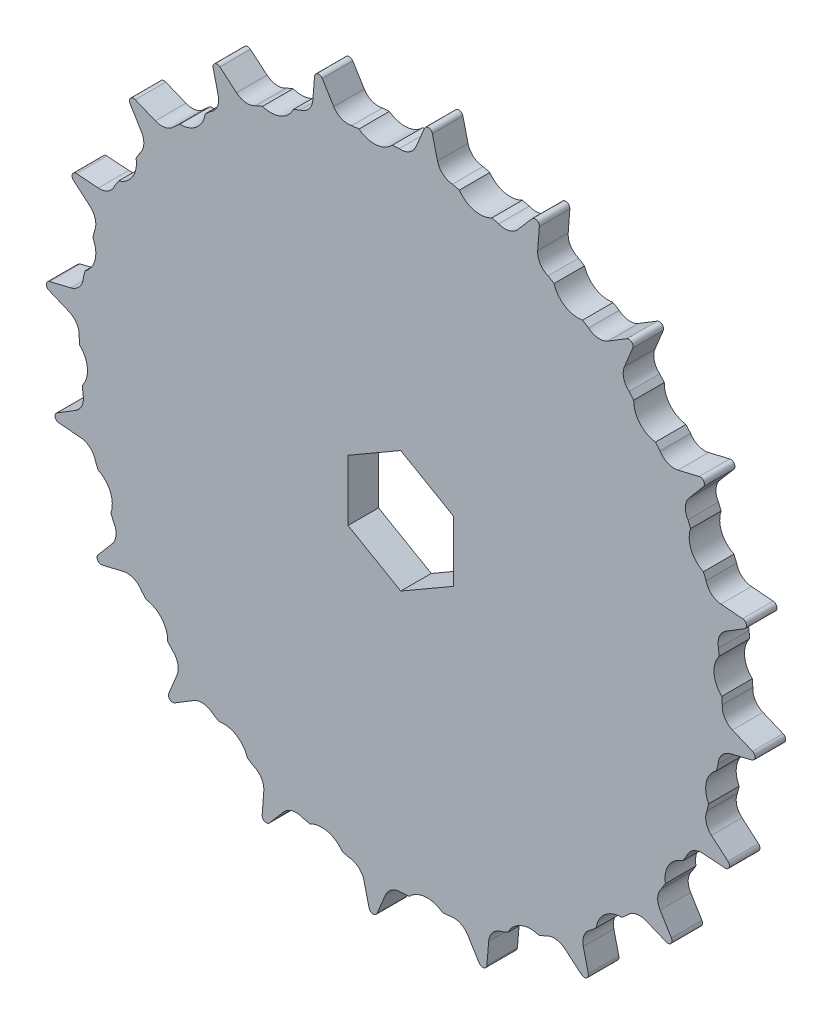
SolidWorks part; units mm, degrees
ref_plane "Front Plane" through (0, 0, 0) normal (0, 0, 1) x (1, 0, 0)
ref_plane "Top Plane" through (0, 0, 0) normal (0, 1, 0) x (1, 0, 0)
ref_plane "Right Plane" through (0, 0, 0) normal (1, 0, 0) x (0, 0, -1)
sketch "Sketch1" plane through (0, 0, 0) normal (0, 0, 1) x (1, 0, 0)
  line L0 (3.6626, 79.3215) -> (5.6677, 84.1262)
  line L1 (3.6626, 79.3215) -> (8.7911, 78.9179) construction
  line L2 (7.5623, 83.9771) -> (8.7911, 78.9179)
  line L3 (3.6626, 79.3215) -> (0, 0) construction
  line L4 (0, 0) -> (8.7911, 78.9179) construction
  line L5 (16.0261, 77.772) -> (18.7582, 82.2038)
  line L6 (20.6061, 81.7602) -> (21.0283, 76.5711)
  line L7 (27.995, 74.3074) -> (31.3867, 78.2573)
  line L8 (33.1425, 77.5301) -> (32.7478, 72.3388)
  line L9 (39.2746, 69.0132) -> (43.2424, 72.3839)
  line L10 (44.8629, 71.3909) -> (43.6609, 66.3253)
  line L11 (49.5871, 62.0196) -> (54.0334, 64.7281)
  line L12 (55.4785, 63.4939) -> (53.4989, 58.6786)
  line L13 (58.6786, 53.4989) -> (63.4939, 55.4785)
  line L14 (64.7281, 54.0334) -> (62.0196, 49.5871)
  line L15 (66.3253, 43.6609) -> (71.3909, 44.8629)
  line L16 (72.3839, 43.2424) -> (69.0132, 39.2746)
  line L17 (72.3388, 32.7478) -> (77.5301, 33.1425)
  line L18 (78.2573, 31.3867) -> (74.3074, 27.995)
  line L19 (76.5711, 21.0283) -> (81.7602, 20.6061)
  line L20 (82.2038, 18.7582) -> (77.772, 16.0261)
  line L21 (78.9179, 8.7911) -> (83.9771, 7.5623)
  line L22 (84.1262, 5.6677) -> (79.3215, 3.6626)
  line L23 (79.3215, -3.6626) -> (84.1262, -5.6677)
  line L24 (83.9771, -7.5623) -> (78.9179, -8.7911)
  line L25 (77.772, -16.0261) -> (82.2038, -18.7582)
  line L26 (81.7602, -20.6061) -> (76.5711, -21.0283)
  line L27 (74.3074, -27.995) -> (78.2573, -31.3867)
  line L28 (77.5301, -33.1425) -> (72.3388, -32.7478)
  line L29 (69.0132, -39.2746) -> (72.3839, -43.2424)
  line L30 (71.3909, -44.8629) -> (66.3253, -43.6609)
  line L31 (62.0196, -49.5871) -> (64.7281, -54.0334)
  line L32 (63.4939, -55.4785) -> (58.6786, -53.4989)
  line L33 (53.4989, -58.6786) -> (55.4785, -63.4939)
  line L34 (54.0334, -64.7281) -> (49.5871, -62.0196)
  line L35 (43.6609, -66.3253) -> (44.8629, -71.3909)
  line L36 (43.2424, -72.3839) -> (39.2746, -69.0132)
  line L37 (32.7478, -72.3388) -> (33.1425, -77.5301)
  line L38 (31.3867, -78.2573) -> (27.995, -74.3074)
  line L39 (21.0283, -76.5711) -> (20.6061, -81.7602)
  line L40 (18.7582, -82.2038) -> (16.0261, -77.772)
  line L41 (8.7911, -78.9179) -> (7.5623, -83.9771)
  line L42 (5.6677, -84.1262) -> (3.6626, -79.3215)
  line L43 (-3.6626, -79.3215) -> (-5.6677, -84.1262)
  line L44 (-7.5623, -83.9771) -> (-8.7911, -78.9179)
  line L45 (-16.0261, -77.772) -> (-18.7582, -82.2038)
  line L46 (-20.6061, -81.7602) -> (-21.0283, -76.5711)
  line L47 (-27.995, -74.3074) -> (-31.3867, -78.2573)
  line L48 (-33.1425, -77.5301) -> (-32.7478, -72.3388)
  line L49 (-39.2746, -69.0132) -> (-43.2424, -72.3839)
  line L50 (-44.8629, -71.3909) -> (-43.6609, -66.3253)
  line L51 (-49.5871, -62.0196) -> (-54.0334, -64.7281)
  line L52 (-55.4785, -63.4939) -> (-53.4989, -58.6786)
  line L53 (-58.6786, -53.4989) -> (-63.4939, -55.4785)
  line L54 (-64.7281, -54.0334) -> (-62.0196, -49.5871)
  line L55 (-66.3253, -43.6609) -> (-71.3909, -44.8629)
  line L56 (-72.3839, -43.2424) -> (-69.0132, -39.2746)
  line L57 (-72.3388, -32.7478) -> (-77.5301, -33.1425)
  line L58 (-78.2573, -31.3867) -> (-74.3074, -27.995)
  line L59 (-76.5711, -21.0283) -> (-81.7602, -20.6061)
  line L60 (-82.2038, -18.7582) -> (-77.772, -16.0261)
  line L61 (-78.9179, -8.7911) -> (-83.9771, -7.5623)
  line L62 (-84.1262, -5.6677) -> (-79.3215, -3.6626)
  line L63 (-79.3215, 3.6626) -> (-84.1262, 5.6677)
  line L64 (-83.9771, 7.5623) -> (-78.9179, 8.7911)
  line L65 (-77.772, 16.0261) -> (-82.2038, 18.7582)
  line L66 (-81.7602, 20.6061) -> (-76.5711, 21.0283)
  line L67 (-74.3074, 27.995) -> (-78.2573, 31.3867)
  line L68 (-77.5301, 33.1425) -> (-72.3388, 32.7478)
  line L69 (-69.0132, 39.2746) -> (-72.3839, 43.2424)
  line L70 (-71.3909, 44.8629) -> (-66.3253, 43.6609)
  line L71 (-62.0196, 49.5871) -> (-64.7281, 54.0334)
  line L72 (-63.4939, 55.4785) -> (-58.6786, 53.4989)
  line L73 (-53.4989, 58.6786) -> (-55.4785, 63.4939)
  line L74 (-54.0334, 64.7281) -> (-49.5871, 62.0196)
  line L75 (-43.6609, 66.3253) -> (-44.8629, 71.3909)
  line L76 (-43.2424, 72.3839) -> (-39.2746, 69.0132)
  line L77 (-32.7478, 72.3388) -> (-33.1425, 77.5301)
  line L78 (-31.3867, 78.2573) -> (-27.995, 74.3074)
  line L79 (-21.0283, 76.5711) -> (-20.6061, 81.7602)
  line L80 (-18.7582, 82.2038) -> (-16.0261, 77.772)
  line L81 (-8.7911, 78.9179) -> (-7.5623, 83.9771)
  line L82 (-5.6677, 84.1262) -> (-3.6626, 79.3215)
  line L83 (0, 80.85) -> (0, 0) construction
  line L84 (0, 0) -> (6.5906, 83.7411) construction
  circle A0 centre (0, 0) radius 80.85 construction
  arc A1 (-3.9676, 80.7526) -> (3.6626, 79.3215) centre (0, 80.85) ccw
  arc A2 (4.2537, 80.738) -> (8.4288, 80.4094) centre (0, 0) cw
  arc A3 (5.6677, 84.1262) -> (7.5623, 83.9771) centre (6.5906, 83.7411) cw
  arc A4 (8.7138, 80.3791) -> (16.0261, 77.772) centre (12.6477, 79.8546) ccw
  arc A5 (18.7582, 82.2038) -> (20.6061, 81.7602) centre (19.6094, 81.6791) cw
  arc A6 (21.1806, 78.0263) -> (27.995, 74.3074) centre (24.984, 76.8929) ccw
  arc A7 (31.3867, 78.2573) -> (33.1425, 77.5301) centre (32.1454, 77.6059) cw
  arc A8 (33.1258, 73.7523) -> (39.2746, 69.0132) centre (36.7051, 72.0379) ccw
  arc A9 (43.2424, 72.3839) -> (44.8629, 71.3909) centre (43.8899, 71.6218) cw
  arc A10 (44.2554, 67.6623) -> (49.5871, 62.0196) centre (47.5224, 65.409) ccw
  arc A11 (54.0334, 64.7281) -> (55.4785, 63.4939) centre (54.5536, 63.8741) cw
  arc A12 (54.2952, 59.9062) -> (58.6786, 53.4989) centre (57.1696, 57.1696) ccw
  arc A13 (63.4939, 55.4785) -> (64.7281, 54.0334) centre (63.8741, 54.5536) cw
  arc A14 (62.9981, 50.675) -> (66.3253, 43.6609) centre (65.409, 47.5224) ccw
  arc A15 (71.3909, 44.8629) -> (72.3839, 43.2424) centre (71.6218, 43.8899) cw
  arc A16 (70.1499, 40.196) -> (72.3388, 32.7478) centre (72.0379, 36.7051) ccw
  arc A17 (77.5301, 33.1425) -> (78.2573, 31.3867) centre (77.6059, 32.1454) cw
  arc A18 (75.5742, 28.7273) -> (76.5711, 21.0283) centre (76.8929, 24.984) ccw
  arc A19 (81.7602, 20.6061) -> (82.2038, 18.7582) centre (81.6791, 19.6094) cw
  arc A20 (79.1377, 16.5512) -> (78.9179, 8.7911) centre (79.8546, 12.6477) ccw
  arc A21 (83.9771, 7.5623) -> (84.1262, 5.6677) centre (83.7411, 6.5906) cw
  arc A22 (80.7526, 3.9676) -> (79.3215, -3.6626) centre (80.85, 0) ccw
  arc A23 (84.1262, -5.6677) -> (83.9771, -7.5623) centre (83.7411, -6.5906) cw
  arc A24 (80.3791, -8.7138) -> (77.772, -16.0261) centre (79.8546, -12.6477) ccw
  arc A25 (82.2038, -18.7582) -> (81.7602, -20.6061) centre (81.6791, -19.6094) cw
  arc A26 (78.0263, -21.1806) -> (74.3074, -27.995) centre (76.8929, -24.984) ccw
  arc A27 (78.2573, -31.3867) -> (77.5301, -33.1425) centre (77.6059, -32.1454) cw
  arc A28 (73.7523, -33.1258) -> (69.0132, -39.2746) centre (72.0379, -36.7051) ccw
  arc A29 (72.3839, -43.2424) -> (71.3909, -44.8629) centre (71.6218, -43.8899) cw
  arc A30 (67.6623, -44.2554) -> (62.0196, -49.5871) centre (65.409, -47.5224) ccw
  arc A31 (64.7281, -54.0334) -> (63.4939, -55.4785) centre (63.8741, -54.5536) cw
  arc A32 (59.9062, -54.2952) -> (53.4989, -58.6786) centre (57.1696, -57.1696) ccw
  arc A33 (55.4785, -63.4939) -> (54.0334, -64.7281) centre (54.5536, -63.8741) cw
  arc A34 (50.675, -62.9981) -> (43.6609, -66.3253) centre (47.5224, -65.409) ccw
  arc A35 (44.8629, -71.3909) -> (43.2424, -72.3839) centre (43.8899, -71.6218) cw
  arc A36 (40.196, -70.1499) -> (32.7478, -72.3388) centre (36.7051, -72.0379) ccw
  arc A37 (33.1425, -77.5301) -> (31.3867, -78.2573) centre (32.1454, -77.6059) cw
  arc A38 (28.7273, -75.5742) -> (21.0283, -76.5711) centre (24.984, -76.8929) ccw
  arc A39 (20.6061, -81.7602) -> (18.7582, -82.2038) centre (19.6094, -81.6791) cw
  arc A40 (16.5512, -79.1377) -> (8.7911, -78.9179) centre (12.6477, -79.8546) ccw
  arc A41 (7.5623, -83.9771) -> (5.6677, -84.1262) centre (6.5906, -83.7411) cw
  arc A42 (3.9676, -80.7526) -> (-3.6626, -79.3215) centre (0, -80.85) ccw
  arc A43 (-5.6677, -84.1262) -> (-7.5623, -83.9771) centre (-6.5906, -83.7411) cw
  arc A44 (-8.7138, -80.3791) -> (-16.0261, -77.772) centre (-12.6477, -79.8546) ccw
  arc A45 (-18.7582, -82.2038) -> (-20.6061, -81.7602) centre (-19.6094, -81.6791) cw
  arc A46 (-21.1806, -78.0263) -> (-27.995, -74.3074) centre (-24.984, -76.8929) ccw
  arc A47 (-31.3867, -78.2573) -> (-33.1425, -77.5301) centre (-32.1454, -77.6059) cw
  arc A48 (-33.1258, -73.7523) -> (-39.2746, -69.0132) centre (-36.7051, -72.0379) ccw
  arc A49 (-43.2424, -72.3839) -> (-44.8629, -71.3909) centre (-43.8899, -71.6218) cw
  arc A50 (-44.2554, -67.6623) -> (-49.5871, -62.0196) centre (-47.5224, -65.409) ccw
  arc A51 (-54.0334, -64.7281) -> (-55.4785, -63.4939) centre (-54.5536, -63.8741) cw
  arc A52 (-54.2952, -59.9062) -> (-58.6786, -53.4989) centre (-57.1696, -57.1696) ccw
  arc A53 (-63.4939, -55.4785) -> (-64.7281, -54.0334) centre (-63.8741, -54.5536) cw
  arc A54 (-62.9981, -50.675) -> (-66.3253, -43.6609) centre (-65.409, -47.5224) ccw
  arc A55 (-71.3909, -44.8629) -> (-72.3839, -43.2424) centre (-71.6218, -43.8899) cw
  arc A56 (-70.1499, -40.196) -> (-72.3388, -32.7478) centre (-72.0379, -36.7051) ccw
  arc A57 (-77.5301, -33.1425) -> (-78.2573, -31.3867) centre (-77.6059, -32.1454) cw
  arc A58 (-75.5742, -28.7273) -> (-76.5711, -21.0283) centre (-76.8929, -24.984) ccw
  arc A59 (-81.7602, -20.6061) -> (-82.2038, -18.7582) centre (-81.6791, -19.6094) cw
  arc A60 (-79.1377, -16.5512) -> (-78.9179, -8.7911) centre (-79.8546, -12.6477) ccw
  arc A61 (-83.9771, -7.5623) -> (-84.1262, -5.6677) centre (-83.7411, -6.5906) cw
  arc A62 (-80.7526, -3.9676) -> (-79.3215, 3.6626) centre (-80.85, 0) ccw
  arc A63 (-84.1262, 5.6677) -> (-83.9771, 7.5623) centre (-83.7411, 6.5906) cw
  arc A64 (-80.3791, 8.7138) -> (-77.772, 16.0261) centre (-79.8546, 12.6477) ccw
  arc A65 (-82.2038, 18.7582) -> (-81.7602, 20.6061) centre (-81.6791, 19.6094) cw
  arc A66 (-78.0263, 21.1806) -> (-74.3074, 27.995) centre (-76.8929, 24.984) ccw
  arc A67 (-78.2573, 31.3867) -> (-77.5301, 33.1425) centre (-77.6059, 32.1454) cw
  arc A68 (-73.7523, 33.1258) -> (-69.0132, 39.2746) centre (-72.0379, 36.7051) ccw
  arc A69 (-72.3839, 43.2424) -> (-71.3909, 44.8629) centre (-71.6218, 43.8899) cw
  arc A70 (-67.6623, 44.2554) -> (-62.0196, 49.5871) centre (-65.409, 47.5224) ccw
  arc A71 (-64.7281, 54.0334) -> (-63.4939, 55.4785) centre (-63.8741, 54.5536) cw
  arc A72 (-59.9062, 54.2952) -> (-53.4989, 58.6786) centre (-57.1696, 57.1696) ccw
  arc A73 (-55.4785, 63.4939) -> (-54.0334, 64.7281) centre (-54.5536, 63.8741) cw
  arc A74 (-50.675, 62.9981) -> (-43.6609, 66.3253) centre (-47.5224, 65.409) ccw
  arc A75 (-44.8629, 71.3909) -> (-43.2424, 72.3839) centre (-43.8899, 71.6218) cw
  arc A76 (-40.196, 70.1499) -> (-32.7478, 72.3388) centre (-36.7051, 72.0379) ccw
  arc A77 (-33.1425, 77.5301) -> (-31.3867, 78.2573) centre (-32.1454, 77.6059) cw
  arc A78 (-28.7273, 75.5742) -> (-21.0283, 76.5711) centre (-24.984, 76.8929) ccw
  arc A79 (-20.6061, 81.7602) -> (-18.7582, 82.2038) centre (-19.6094, 81.6791) cw
  arc A80 (-16.5512, 79.1377) -> (-8.7911, 78.9179) centre (-12.6477, 79.8546) ccw
  arc A81 (-7.5623, 83.9771) -> (-5.6677, 84.1262) centre (-6.5906, 83.7411) cw
  point P289 (0, 0)
  dimension "D1" = 161.7
  dimension "D2" = 3.9688
  dimension "D5" = 1
  dimension "D6" = 84
  dimension "D3" = 4.5
  dimension "D4" = 40
extrude "Boss-Extrude1" add sketch "Sketch1" along normal blind 7.3 contours A81 L81 A80 L80 A79 L79 A78 L78 A77 L77 A76 L76 A75 L75 A74 L74 A73 L73 A72 L72 A71 L71 A70 L70 A69 L69 A68 L68 A67 L67 A66 L66 A65 L65 A64 L64 A63 L63 A62 L62 A61 L61 A60 L60 A59 L59 A58 L58 A57 L57 A56 | A3 L0 A2 L2
sketch "Sketch2" plane through (0, 0, 7.3) normal (0, 0, 1) x (1, 0, 0)
  circle A0 centre (0, 0) radius 12.5
  dimension "D1" = 25
extrude "Boss-Extrude2" add sketch "Sketch2" along normal blind 40
fillet "Fillet1" radius 30 1 edges at (12.5, 0, 7.3)
sketch "Sketch3" plane through (0, 0, 47.3) normal (0, 0, 1) x (1, 0, 0)
  circle A0 centre (0, 0) radius 5
  dimension "D1" = 10
extrude "Cut-Extrude1" cut sketch "Sketch3" against normal through all
hole_wizard "Ø1.0mm Dowel Hole1" positions "3DSketch1" profile "Sketch4" hole size "Ø1.0" standard "ANSI Metric"
sketch3d "3DSketch1"
  point P0 (-6.8176, -10.4771, 42.0201)
  point P2 (-11.0684, 5.8086, 41.6583)
sketch "Sketch4" plane through (-6.8176, -10.4771, 42.0201) normal (0, 0, 1) x (0.8382, -0.5454, 0)
  line L0 (0, 0) -> (0, 34)
  line L1 (0, 34) -> (1.4, 33.1588)
  line L2 (1.4, 33.1588) -> (1.4, 0)
  line L5 (1.4, 0) -> (0, 0)
  line L10 (0, 34) -> (-1.4, 33.1588) construction
  line L11 (0, -6.35) -> (0, 107.95) construction
  dimension "Hole Dia." = 2.8
  dimension "Hole Depth" = 34
  dimension "Drill Angle" = 118
sketch "Sketch5" plane through (0, 0, 0) normal (0, 0, -1) x (-1, 0, 0)
  line L0 (-0.9617, 76.9995) -> (2.0291, 76.7641)
  line L1 (-0.9617, 76.9995) -> (-0.3094, 85.2872)
  line L2 (12.9952, 75.9011) -> (13.6474, 84.1888)
  line L3 (-0.3094, 85.2872) -> (13.6474, 84.1888)
  line L4 (10.0044, 76.1365) -> (12.9952, 75.9011)
  arc A0 (2.0291, 76.7641) -> (10.0044, 76.1365) centre (6.3676, 80.9087) ccw
  arc A2 (7.5623, 83.9771) -> (5.6677, 84.1262) centre (6.5906, 83.7411) ccw construction
  arc A3 (-3.6626, 79.3215) -> (3.6626, 79.3215) centre (0, 80.85) ccw construction
  arc A4 (8.7911, 78.9179) -> (16.0261, 77.772) centre (12.6477, 79.8546) ccw construction
  point P17 (6.669, 84.738)
  dimension "D2" = 3
  dimension "D3" = 3
  dimension "D4" = 6
  dimension "D1" = 14
extrude "Cut-Extrude2" cut sketch "Sketch5" against normal blind 10
pattern_circular "CirPattern1" count 20 over 360 about axis through (0, 0, 0) along (0, 0, 1) of "Cut-Extrude2"
sketch "Sketch6" plane through (0, 0, 0) normal (0, 1, 0) x (1, 0, 0)
  line L0 (-84.7411, -7.3) -> (-83.9771, -7.3) construction
  line L1 (-84.3591, -7.3) -> (85.648, -7.3)
  line L2 (-84.3591, -7.3) -> (-84.3591, -52.0573)
  line L3 (-84.3591, -52.0573) -> (85.648, -52.0573)
  line L4 (85.648, -7.3) -> (85.648, -52.0573)
extrude "Cut-Extrude3" cut sketch "Sketch6" against normal through all both and the other way through all
sketch "Sketch7" plane through (0, 0, 0) normal (0, 0, -1) x (-1, 0, 0)
  line L1 (12.6, -7.2746) -> (12.6, 7.2746)
  line L2 (12.6, 7.2746) -> (0, 14.5492)
  line L3 (0, 14.5492) -> (-12.6, 7.2746)
  line L4 (-12.6, 7.2746) -> (-12.6, -7.2746)
  line L5 (-12.6, -7.2746) -> (0, -14.5492)
  line L6 (0, -14.5492) -> (12.6, -7.2746)
  circle A0 centre (0, 0) radius 12.6 construction
  point P1 (0, 0)
  point P10 (0, 0)
  dimension "D1" = 25.2
extrude "Cut-Extrude4" cut sketch "Sketch7" against normal through all both
